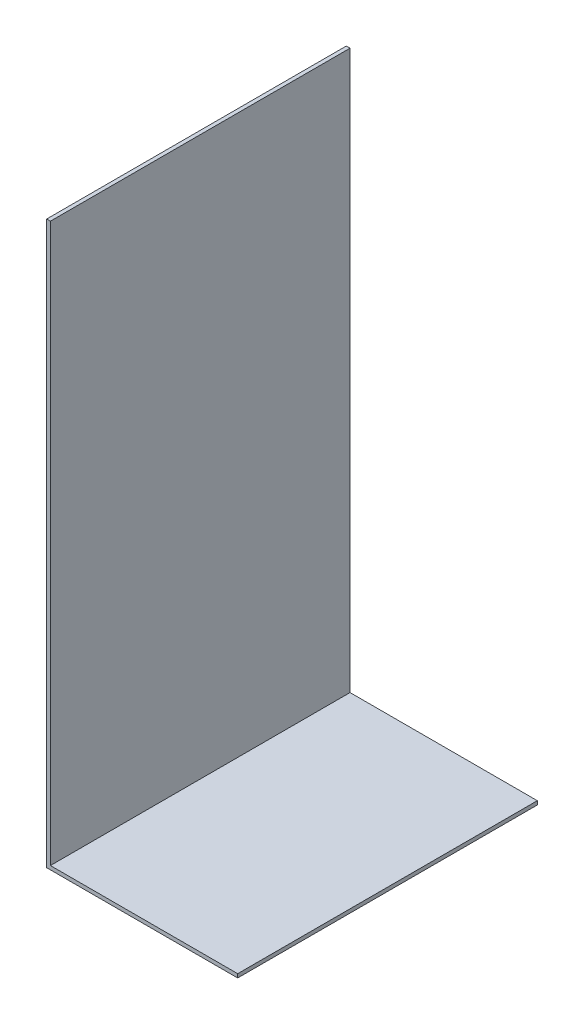
SolidWorks part; units mm, degrees
ref_plane "Front Plane" through (0, 0, 0) normal (0, 0, 1) x (1, 0, 0)
ref_plane "Top Plane" through (0, 0, 0) normal (0, 1, 0) x (1, 0, 0)
ref_plane "Right Plane" through (0, 0, 0) normal (1, 0, 0) x (0, 0, -1)
sketch "Sketch1" plane through (0, 0, 0) normal (0, 1, 0) x (1, 0, 0)
  line L1 (-25, 40) -> (25, 40)
  line L2 (-25, 40) -> (-25, -40)
  line L3 (-25, -40) -> (25, -40)
  line L4 (25, 40) -> (25, -40)
  line L5 (-25, 40) -> (25, -40) construction
  line L6 (-25, -40) -> (25, 40) construction
  point P0 (0, 0)
  dimension "D1" = 50
  dimension "D2" = 80
extrude "Boss-Extrude1" add sketch "Sketch1" along normal blind 1
sketch "Sketch3" plane through (-25, 0, 0) normal (-1, 0, 0) x (0, 0, 1)
  line L2 (40, 0) -> (-40, 0)
  line L3 (40, 0) -> (40, 150)
  line L4 (40, 150) -> (-40, 150)
  line L5 (-40, 0) -> (-40, 150)
  line L7 (-40, 1) -> (40, 1) construction
  dimension "D1" = 150
extrude "Boss-Extrude2" add sketch "Sketch3" along normal blind 1
